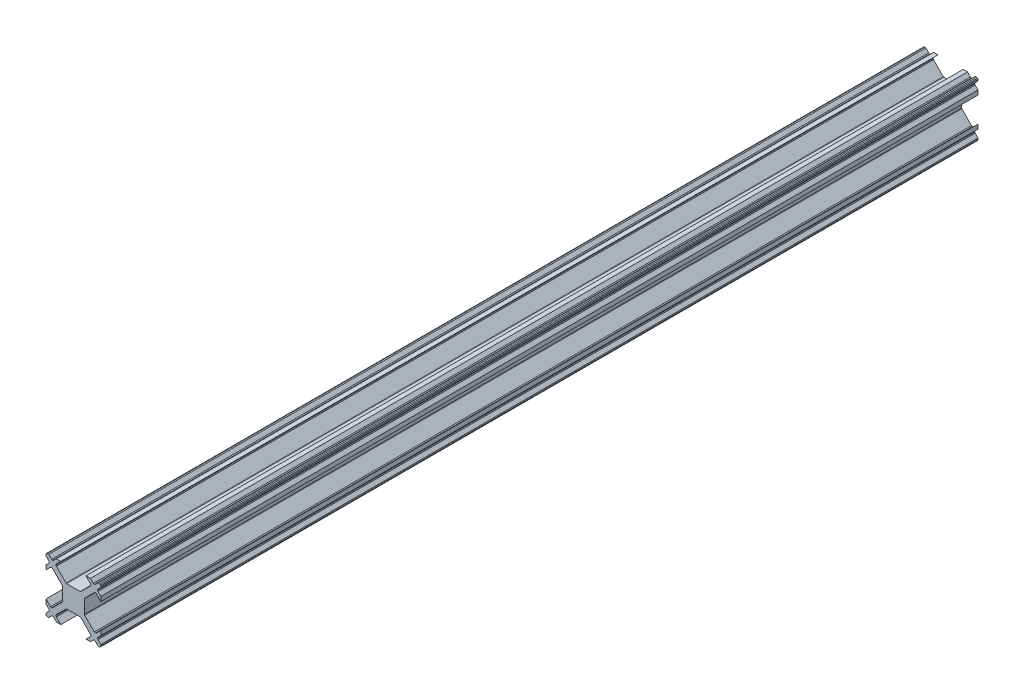
SolidWorks part; units mm, degrees
ref_plane "Front Plane" through (0, 0, 0) normal (0, 0, 1) x (1, 0, 0)
ref_plane "Top Plane" through (0, 0, 0) normal (0, 1, 0) x (1, 0, 0)
ref_plane "Right Plane" through (0, 0, 0) normal (1, 0, 0) x (0, 0, -1)
ref_plane "Plane1" through (0, 0, 12.5) normal (0, 0, 1) x (1, 0, 0)
sketch "Sketch1" plane through (0, 0, 12.5) normal (0, 0, 1) x (1, 0, 0)
  line L0 (1.3661, 2.0732) -> (1.285, 2.0191)
  line L1 (1.285, 2.0191) -> (1.1893, 2)
  line L2 (1.1893, 2) -> (-1.1893, 2)
  line L3 (-1.1893, 2) -> (-1.285, 2.0191)
  line L4 (-1.285, 2.0191) -> (-1.3661, 2.0732)
  line L5 (-1.3661, 2.0732) -> (-3.1161, 3.8232)
  line L6 (-3.1161, 3.8232) -> (-3.1893, 4)
  line L7 (-3.1893, 4) -> (-3.1161, 4.1768)
  line L8 (-3.1161, 4.1768) -> (-2.2929, 5)
  line L9 (-2.2929, 5) -> (-3.095, 5)
  line L10 (-3.095, 5) -> (-3.6232, 4.4718)
  line L11 (-3.6232, 4.4718) -> (-3.8, 4.3985)
  line L12 (-3.8, 4.3985) -> (-3.9768, 4.4718)
  line L13 (-3.9768, 4.4718) -> (-4.505, 5)
  line L14 (-4.505, 5) -> (-4.75, 5)
  line L15 (-4.75, 5) -> (-4.9268, 4.9268)
  line L16 (-4.9268, 4.9268) -> (-5, 4.75)
  line L17 (-5, 4.75) -> (-5, 4.505)
  line L18 (-5, 4.505) -> (-4.4718, 3.9768)
  line L19 (-4.4718, 3.9768) -> (-4.3985, 3.8)
  line L20 (-4.3985, 3.8) -> (-4.4718, 3.6232)
  line L21 (-4.4718, 3.6232) -> (-5, 3.095)
  line L22 (-5, 3.095) -> (-5, 2.2929)
  line L23 (-5, 2.2929) -> (-4.1768, 3.1161)
  line L24 (-4.1768, 3.1161) -> (-4, 3.1893)
  line L25 (-4, 3.1893) -> (-3.8232, 3.1161)
  line L26 (-3.8232, 3.1161) -> (-2.0732, 1.3661)
  line L27 (-2.0732, 1.3661) -> (-2.0191, 1.285)
  line L28 (-2.0191, 1.285) -> (-2, 1.1893)
  line L29 (-2, 1.1893) -> (-2, -1.1893)
  line L30 (-2, -1.1893) -> (-2.0191, -1.285)
  line L31 (-2.0191, -1.285) -> (-2.0732, -1.3661)
  line L32 (-2.0732, -1.3661) -> (-3.8232, -3.1161)
  line L33 (-3.8232, -3.1161) -> (-4, -3.1893)
  line L34 (-4, -3.1893) -> (-4.1768, -3.1161)
  line L35 (-4.1768, -3.1161) -> (-5, -2.2929)
  line L36 (-5, -2.2929) -> (-5, -3.095)
  line L37 (-5, -3.095) -> (-4.4718, -3.6232)
  line L38 (-4.4718, -3.6232) -> (-4.3985, -3.8)
  line L39 (-4.3985, -3.8) -> (-4.4718, -3.9768)
  line L40 (-4.4718, -3.9768) -> (-5, -4.505)
  line L41 (-5, -4.505) -> (-5, -4.75)
  line L42 (-5, -4.75) -> (-4.9268, -4.9268)
  line L43 (-4.9268, -4.9268) -> (-4.75, -5)
  line L44 (-4.75, -5) -> (-4.505, -5)
  line L45 (-4.505, -5) -> (-3.9768, -4.4718)
  line L46 (-3.9768, -4.4718) -> (-3.8, -4.3985)
  line L47 (-3.8, -4.3985) -> (-3.6232, -4.4718)
  line L48 (-3.6232, -4.4718) -> (-3.095, -5)
  line L49 (-3.095, -5) -> (-2.2929, -5)
  line L50 (-2.2929, -5) -> (-3.1161, -4.1768)
  line L51 (-3.1161, -4.1768) -> (-3.1893, -4)
  line L52 (-3.1893, -4) -> (-3.1161, -3.8232)
  line L53 (-3.1161, -3.8232) -> (-1.3661, -2.0732)
  line L54 (-1.3661, -2.0732) -> (-1.285, -2.0191)
  line L55 (-1.285, -2.0191) -> (-1.1893, -2)
  line L56 (-1.1893, -2) -> (1.1893, -2)
  line L57 (1.1893, -2) -> (1.285, -2.0191)
  line L58 (1.285, -2.0191) -> (1.3661, -2.0732)
  line L59 (1.3661, -2.0732) -> (3.1161, -3.8232)
  line L60 (3.1161, -3.8232) -> (3.1893, -4)
  line L61 (3.1893, -4) -> (3.1161, -4.1768)
  line L62 (3.1161, -4.1768) -> (2.2929, -5)
  line L63 (2.2929, -5) -> (3.095, -5)
  line L64 (3.095, -5) -> (3.6232, -4.4718)
  line L65 (3.6232, -4.4718) -> (3.8, -4.3985)
  line L66 (3.8, -4.3985) -> (3.9768, -4.4718)
  line L67 (3.9768, -4.4718) -> (4.505, -5)
  line L68 (4.505, -5) -> (4.75, -5)
  line L69 (4.75, -5) -> (4.9268, -4.9268)
  line L70 (4.9268, -4.9268) -> (5, -4.75)
  line L71 (5, -4.75) -> (5, -4.505)
  line L72 (5, -4.505) -> (4.4718, -3.9768)
  line L73 (4.4718, -3.9768) -> (4.3985, -3.8)
  line L74 (4.3985, -3.8) -> (4.4718, -3.6232)
  line L75 (4.4718, -3.6232) -> (5, -3.095)
  line L76 (5, -3.095) -> (5, -2.2929)
  line L77 (5, -2.2929) -> (4.1768, -3.1161)
  line L78 (4.1768, -3.1161) -> (4, -3.1893)
  line L79 (4, -3.1893) -> (3.8232, -3.1161)
  line L80 (3.8232, -3.1161) -> (2.0732, -1.3661)
  line L81 (2.0732, -1.3661) -> (2.0191, -1.285)
  line L82 (2.0191, -1.285) -> (2, -1.1893)
  line L83 (2, -1.1893) -> (2, 1.1893)
  line L84 (2, 1.1893) -> (2.0191, 1.285)
  line L85 (2.0191, 1.285) -> (2.0732, 1.3661)
  line L86 (2.0732, 1.3661) -> (3.8232, 3.1161)
  line L87 (3.8232, 3.1161) -> (4, 3.1893)
  line L88 (4, 3.1893) -> (4.1768, 3.1161)
  line L89 (4.1768, 3.1161) -> (5, 2.2929)
  line L90 (5, 2.2929) -> (5, 3.095)
  line L91 (5, 3.095) -> (4.4718, 3.6232)
  line L92 (4.4718, 3.6232) -> (4.3985, 3.8)
  line L93 (4.3985, 3.8) -> (4.4718, 3.9768)
  line L94 (4.4718, 3.9768) -> (5, 4.505)
  line L95 (5, 4.505) -> (5, 4.75)
  line L96 (5, 4.75) -> (4.9268, 4.9268)
  line L97 (4.9268, 4.9268) -> (4.75, 5)
  line L98 (4.75, 5) -> (4.505, 5)
  line L99 (4.505, 5) -> (3.9768, 4.4718)
  line L100 (3.9768, 4.4718) -> (3.8, 4.3985)
  line L101 (3.8, 4.3985) -> (3.6232, 4.4718)
  line L102 (3.6232, 4.4718) -> (3.095, 5)
  line L103 (3.095, 5) -> (2.2929, 5)
  line L104 (2.2929, 5) -> (3.1161, 4.1768)
  line L105 (3.1161, 4.1768) -> (3.1893, 4)
  line L106 (3.1893, 4) -> (3.1161, 3.8232)
  line L107 (3.1161, 3.8232) -> (1.3661, 2.0732)
extrude "Boss-Extrude1" add sketch "Sketch1" against normal blind 160
